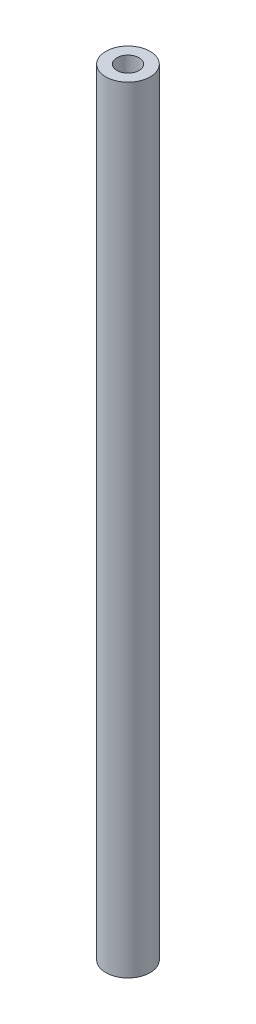
SolidWorks part; units mm, degrees
ref_plane "Front Plane" through (0, 0, 0) normal (0, 0, 1) x (1, 0, 0)
ref_plane "Top Plane" through (0, 0, 0) normal (0, 1, 0) x (1, 0, 0)
ref_plane "Right Plane" through (0, 0, 0) normal (1, 0, 0) x (0, 0, -1)
sketch "Sketch2" plane through (0, 0, 0) normal (0, 1, 0) x (1, 0, 0)
  circle A0 centre (0, 0) radius 5
extrude "Boss-Extrude2" add sketch "Sketch2" along normal blind 175
hole_wizard "M6 Tapped Hole1" positions "Sketch3" profile "Sketch4" tap size "M6" standard "DIN"
sketch "Sketch3" plane through (0, 175, 0) normal (0, 1, 0) x (1, 0, 0)
  point P0 (0, 0)
  point P3 (0, 0)
sketch "Sketch4" plane through (0, 175, 0) normal (1, 0, 0) x (0, 0, 1)
  line L0 (0, 0) -> (0, 17.5022)
  line L1 (0, 17.5022) -> (2.5, 16)
  line L2 (2.5, 16) -> (2.5, 0)
  line L5 (2.5, 0) -> (0, 0)
  line L10 (0, 17.5022) -> (-2.5, 16) construction
  line L11 (0, -6.35) -> (0, 107.95) construction
  dimension "Tap Drill Dia." = 5
  dimension "Tap Drill Depth" = 16
  dimension "Drill Angle" = 118
cosmetic thread "Hole Thread1" parameters "D1"=10, "D2"=6
cosmetic thread "Hole Thread2" parameters "D1"=10, "D2"=6
hole_wizard "M6 Tapped Hole2" positions "Sketch5" profile "Sketch6" tap size "M6" standard "DIN"
sketch "Sketch5" plane through (0, 0, 0) normal (0, -1, 0) x (-1, 0, 0)
  point P0 (0, 0)
  point P3 (0, 0)
sketch "Sketch6" plane through (0, 0, 0) normal (1, 0, 0) x (0, 0, -1)
  line L0 (0, 0) -> (0, 17.5022)
  line L1 (0, 17.5022) -> (2.5, 16)
  line L2 (2.5, 16) -> (2.5, 0)
  line L5 (2.5, 0) -> (0, 0)
  line L10 (0, 17.5022) -> (-2.5, 16) construction
  line L11 (0, -6.35) -> (0, 107.95) construction
  dimension "Tap Drill Dia." = 5
  dimension "Tap Drill Depth" = 16
  dimension "Drill Angle" = 118
cosmetic thread "Hole Thread3" parameters "D1"=10, "D2"=6
cosmetic thread "Hole Thread4" parameters "D1"=10, "D2"=6
